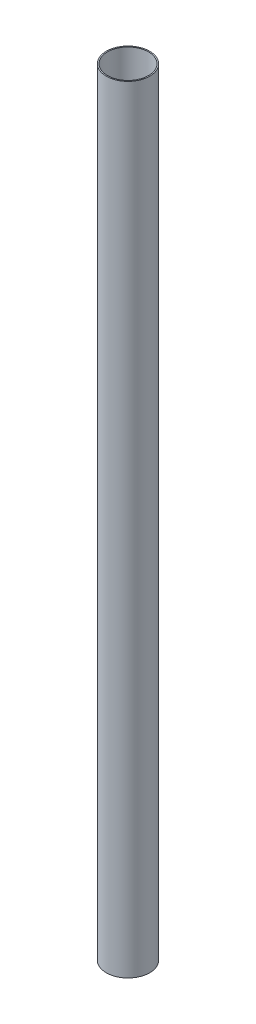
SolidWorks part; units mm, degrees
ref_plane "Front Plane" through (0, 0, 0) normal (0, 0, 1) x (1, 0, 0)
ref_plane "Top Plane" through (0, 0, 0) normal (0, 1, 0) x (1, 0, 0)
ref_plane "Right Plane" through (0, 0, 0) normal (1, 0, 0) x (0, 0, -1)
sketch "Sketch1" plane through (0, 0, 0) normal (0, 0, 1) x (1, 0, 0)
  line L1 (26.9748, 1019.9878) -> (28.4988, 1019.9878)
  line L2 (26.9748, 1019.9878) -> (26.9748, 0)
  line L3 (26.9748, 0) -> (28.4988, 0)
  line L4 (28.4988, 1019.9878) -> (28.4988, 0)
  dimension "D1" = 0
  dimension "D2" = 26.9748
  dimension "D3" = 1.524
  dimension "D4" = 1019.9878
ref_axis "Central Axis" through (0, 1146.81, 0) along (0, -1, 0)
revolve "Revolve1" add sketch "Sketch1" angle 360 about axis through (0, 1146.81, 0) along (0, -1, 0)
